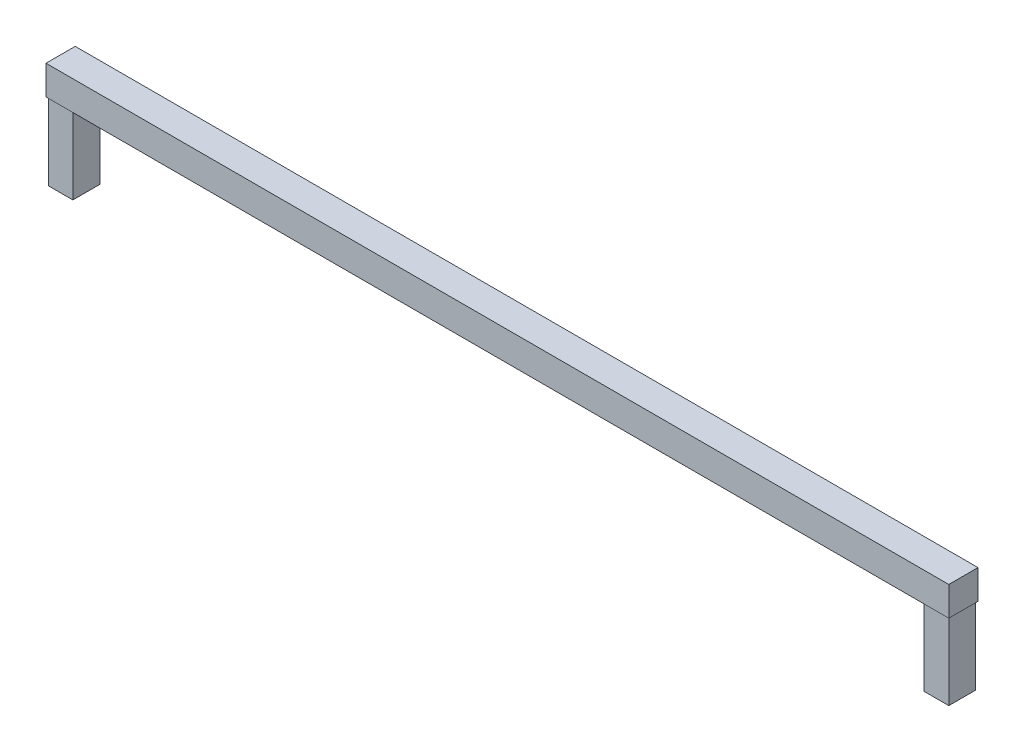
SolidWorks part; units mm, degrees
ref_plane "Front Plane" through (0, 0, 0) normal (0, 0, 1) x (1, 0, 0)
ref_plane "Top Plane" through (0, 0, 0) normal (0, 1, 0) x (1, 0, 0)
ref_plane "Right Plane" through (0, 0, 0) normal (1, 0, 0) x (0, 0, -1)
sketch "Sketch2" plane through (0, 0, 0) normal (0, 0, 1) x (1, 0, 0)
  line L0 (0, 0) -> (0, -220.6984) construction
  line L1 (0, 0) -> (-587, 0)
  dimension "D1" = 587
extrude "Extrude-Thin1" add sketch "Sketch2" along normal blind 38 thin
sketch "Sketch3" plane through (0, 0, 0) normal (0, -1, 0) x (1, 0, 0)
  line L0 (-587, 38) -> (-587, 0) construction
  line L1 (-553.55, 1.5) -> (-585.5, 1.5)
  line L2 (-553.55, 1.5) -> (-553.55, 36.5)
  line L3 (-553.55, 36.5) -> (-585.5, 36.5)
  line L4 (-585.5, 1.5) -> (-585.5, 36.5)
  line L5 (0, 0) -> (-587, 0) construction
  line L6 (0, 38) -> (-587, 38) construction
  dimension "D1" = 1.5
  dimension "D2" = 1.5
  dimension "D3" = 1.5
  dimension "D4" = 31.95
extrude "Boss-Extrude1" add sketch "Sketch3" along normal blind 100
mirror "Mirror1" about plane through (0, 38, 38) normal (1, 0, 0) of bodies 102
